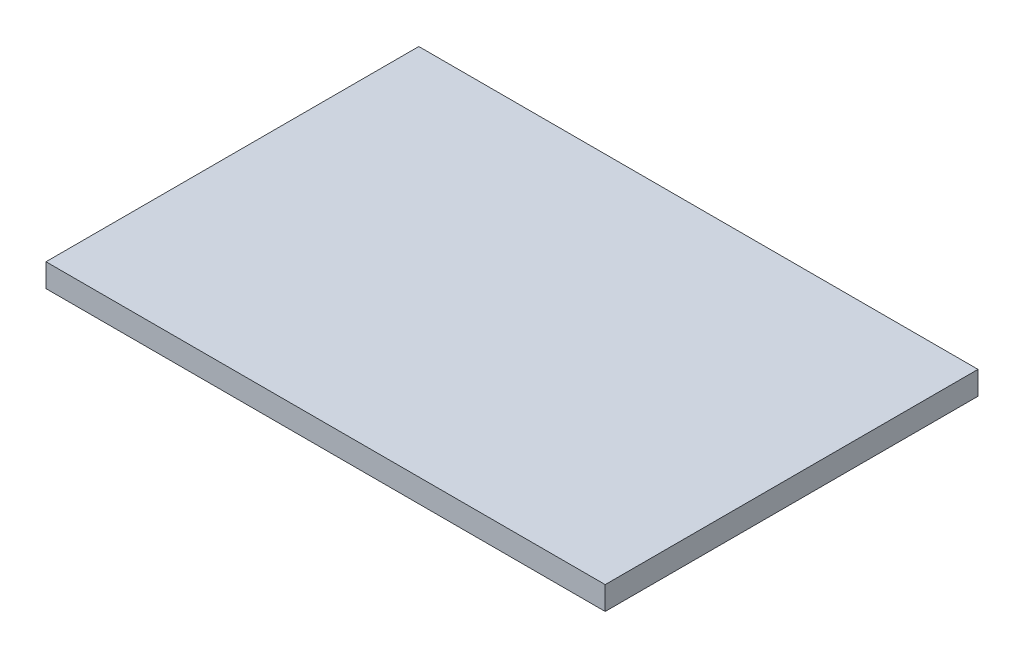
SolidWorks part; units mm, degrees
ref_plane "Front Plane" through (0, 0, 0) normal (0, 0, 1) x (1, 0, 0)
ref_plane "Top Plane" through (0, 0, 0) normal (0, 1, 0) x (1, 0, 0)
ref_plane "Right Plane" through (0, 0, 0) normal (1, 0, 0) x (0, 0, -1)
sketch "Sketch1" plane through (0, 0, 0) normal (0, 1, 0) x (1, 0, 0)
  line L1 (0, 0) -> (152.4, 0)
  line L2 (0, 0) -> (0, 101.6)
  line L3 (0, 101.6) -> (152.4, 101.6)
  line L4 (152.4, 0) -> (152.4, 101.6)
  dimension "D1" = 152.4
  dimension "D2" = 101.6
extrude "Boss-Extrude1" add sketch "Sketch1" along normal blind 6.35
